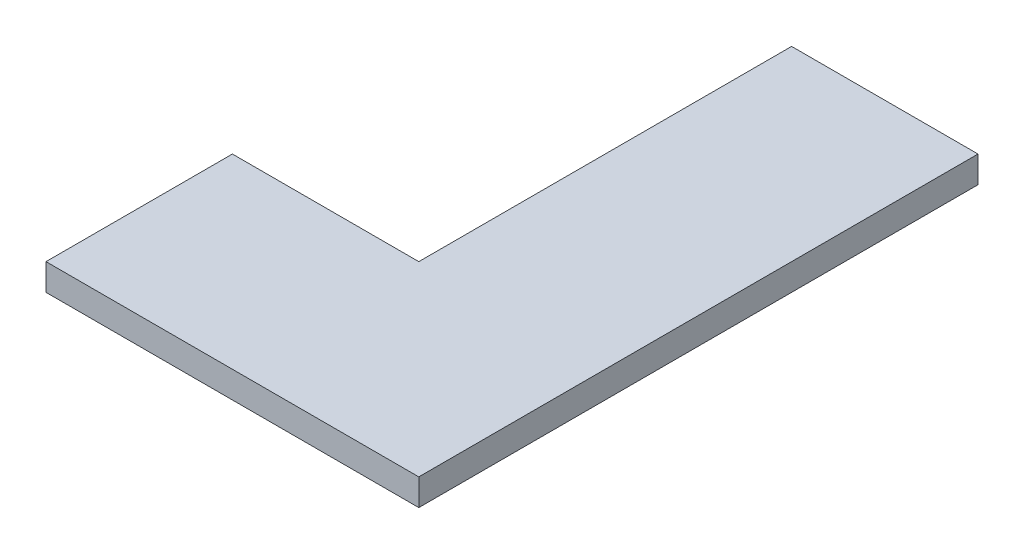
SolidWorks part; units mm, degrees
ref_plane "Front Plane" through (0, 0, 0) normal (0, 0, 1) x (1, 0, 0)
ref_plane "Top Plane" through (0, 0, 0) normal (0, 1, 0) x (1, 0, 0)
ref_plane "Right Plane" through (0, 0, 0) normal (1, 0, 0) x (0, 0, -1)
sketch "Sketch1" plane through (0, 0, 0) normal (0, 1, 0) x (1, 0, 0)
  line L0 (-70, 105) -> (70, -105) construction
  line L1 (-70, 105) -> (70, 105) construction
  line L2 (-70, 105) -> (-70, -105) construction
  line L3 (-70, -105) -> (70, -105) construction
  line L4 (70, 105) -> (70, -105) construction
  line L5 (0, 105) -> (70, 105)
  line L6 (70, 105) -> (70, -105)
  line L7 (70, -105) -> (-70, -105)
  line L8 (-70, -105) -> (-70, -35)
  line L9 (-70, -35) -> (0, -35)
  line L10 (0, -35) -> (0, 105)
  dimension "D1" = 140
  dimension "D2" = 210
  dimension "D3" = 70
extrude "Boss-Extrude1" add sketch "Sketch1" along normal blind 10
